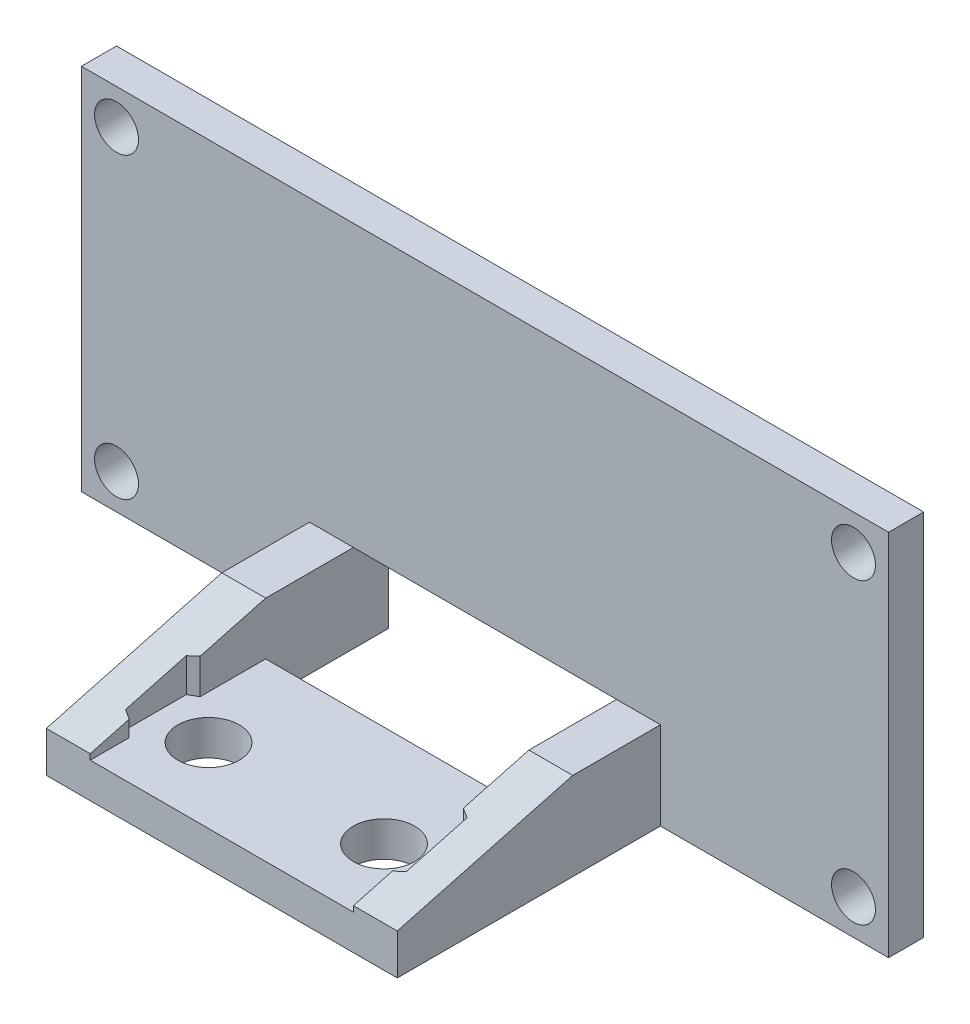
SolidWorks part; units mm, degrees
ref_plane "Front Plane" through (0, 0, 0) normal (0, 0, 1) x (1, 0, 0)
ref_plane "Top Plane" through (0, 0, 0) normal (0, 1, 0) x (1, 0, 0)
ref_plane "Right Plane" through (0, 0, 0) normal (1, 0, 0) x (0, 0, -1)
sketch "Sketch1" plane through (0, 0, 0) normal (0, 0, 1) x (1, 0, 0)
  line L1 (-23, 10.5) -> (23, 10.5)
  line L2 (-23, 10.5) -> (-23, -10.5)
  line L3 (-23, -10.5) -> (23, -10.5)
  line L4 (23, 10.5) -> (23, -10.5)
  line L5 (-23, 10.5) -> (23, -10.5) construction
  line L6 (-23, -10.5) -> (23, 10.5) construction
  line L7 (-7.5, -5.5) -> (7.5, -5.5)
  line L8 (-7.5, -5.5) -> (-7.5, -15.5)
  line L9 (-7.5, -15.5) -> (7.5, -15.5)
  line L10 (7.5, -5.5) -> (7.5, -15.5)
  line L11 (-7.5, -5.5) -> (7.5, -15.5) construction
  line L12 (-7.5, -15.5) -> (7.5, -5.5) construction
  point P0 (0, 0)
  point P6 (0, -10.5)
  dimension "D1" = 46
  dimension "D2" = 21
  dimension "D3" = 15
  dimension "D4" = 10
extrude "Boss-Extrude1" add sketch "Sketch1" along normal blind 2 contours L7 L10 L3 L4 L1 L2 L8
sketch "Sketch2" plane through (0, 0, 2) normal (0, 0, 1) x (1, 0, 0)
  line L0 (-23, -10.5) -> (-7.5, -10.5) construction
  line L1 (-10, -10.5) -> (-7.5, -10.5)
  line L2 (-10, -10.5) -> (-10, -5.5)
  line L3 (-10, -5.5) -> (-7.5, -5.5)
  line L4 (-7.5, -10.5) -> (-7.5, -5.5)
  line L5 (-7.5, -5.5) -> (-7.5, -10.5) construction
  line L6 (-7.5, -5.5) -> (7.5, -5.5) construction
  line L7 (7.5, -10.5) -> (10, -10.5)
  line L8 (7.5, -10.5) -> (7.5, -5.5)
  line L9 (7.5, -5.5) -> (10, -5.5)
  line L10 (10, -10.5) -> (10, -5.5)
  dimension "D1" = 20
  dimension "D2" = 10
  dimension "D3" = 5
extrude "Boss-Extrude2" add sketch "Sketch2" along normal blind 15
sketch "Sketch5" plane through (0, 0, 17) normal (0, 0, 1) x (1, 0, 0)
  line L0 (7.5, -5.5) -> (7.5, -10.5) construction
  line L1 (-7.5, -10.5) -> (7.5, -10.5)
  line L2 (-7.5, -10.5) -> (-7.5, -8.5)
  line L3 (-7.5, -8.5) -> (7.5, -8.5)
  line L4 (7.5, -10.5) -> (7.5, -8.5)
  dimension "D1" = 2
extrude "Boss-Extrude3" add sketch "Sketch5" against normal blind 10
chamfer "Chamfer1" distance 10 angle 15 2 edges at (8.75, -5.5, 17) (-8.75, -5.5, 17)
sketch "Sketch6" plane through (0, 0, 0) normal (0, 0, -1) x (-1, 0, 0)
  line L0 (-23, 10.5) -> (-23, -10.5) construction
  line L2 (-7.5, -10.5) -> (-23, -10.5) construction
  line L3 (23, 10.5) -> (-23, 10.5) construction
  line L4 (23, 10.5) -> (23, -10.5) construction
  line L6 (23, -10.5) -> (7.5, -10.5) construction
  circle A0 centre (21, 8.5) radius 1.25
  circle A1 centre (-21, -8.5) radius 1.25
  circle A2 centre (-21, 8.5) radius 1.25
  circle A3 centre (21, -8.5) radius 1.25
  dimension "D5" = 2.5
  dimension "D6" = 2.5
  dimension "D9" = 2.5
  dimension "D11" = 2.5
  dimension "D1" = 2
  dimension "D2" = 2
  dimension "D3" = 2
  dimension "D4" = 2
  dimension "D7" = 2
  dimension "D8" = 2
  dimension "D10" = 2
  dimension "D12" = 2
extrude "Cut-Extrude1" cut sketch "Sketch6" against normal through all
sketch "Sketch7" plane through (0, -8.5, 0) normal (0, 1, 0) x (1, 0, 0)
  line L0 (-5, -12.7559) -> (5, -12.7559) construction
  line L1 (0, -12.7559) -> (0, 0) construction
  circle A0 centre (-5, -12.7559) radius 1.75
  circle A1 centre (5, -12.7559) radius 1.75
  dimension "D1" = 3.5
  dimension "D2" = 3.5
  dimension "D3" = 10
extrude "Cut-Extrude2" cut sketch "Sketch7" against normal through all
sketch "Sketch8" plane through (0, -8.5, 0) normal (0, 1, 0) x (1, 0, 0)
  line L1 (5, -16.22) -> (8, -14.488)
  line L2 (8, -14.488) -> (8, -11.0239)
  line L3 (8, -11.0239) -> (5, -9.2918)
  line L4 (5, -9.2918) -> (2, -11.0239)
  line L5 (2, -11.0239) -> (2, -14.488)
  line L6 (2, -14.488) -> (5, -16.22)
  line L7 (-5, -16.22) -> (-2, -14.488)
  line L8 (-2, -14.488) -> (-2, -11.0239)
  line L9 (-2, -11.0239) -> (-5, -9.2918)
  line L10 (-5, -9.2918) -> (-8, -11.0239)
  line L11 (-8, -11.0239) -> (-8, -14.488)
  line L12 (-8, -14.488) -> (-5, -16.22)
  circle A0 centre (5, -12.7559) radius 3 construction
  circle A1 centre (-5, -12.7559) radius 3 construction
  dimension "D1" = 6
  dimension "D2" = 6
extrude "Cut-Extrude3" cut sketch "Sketch8" along normal through all
